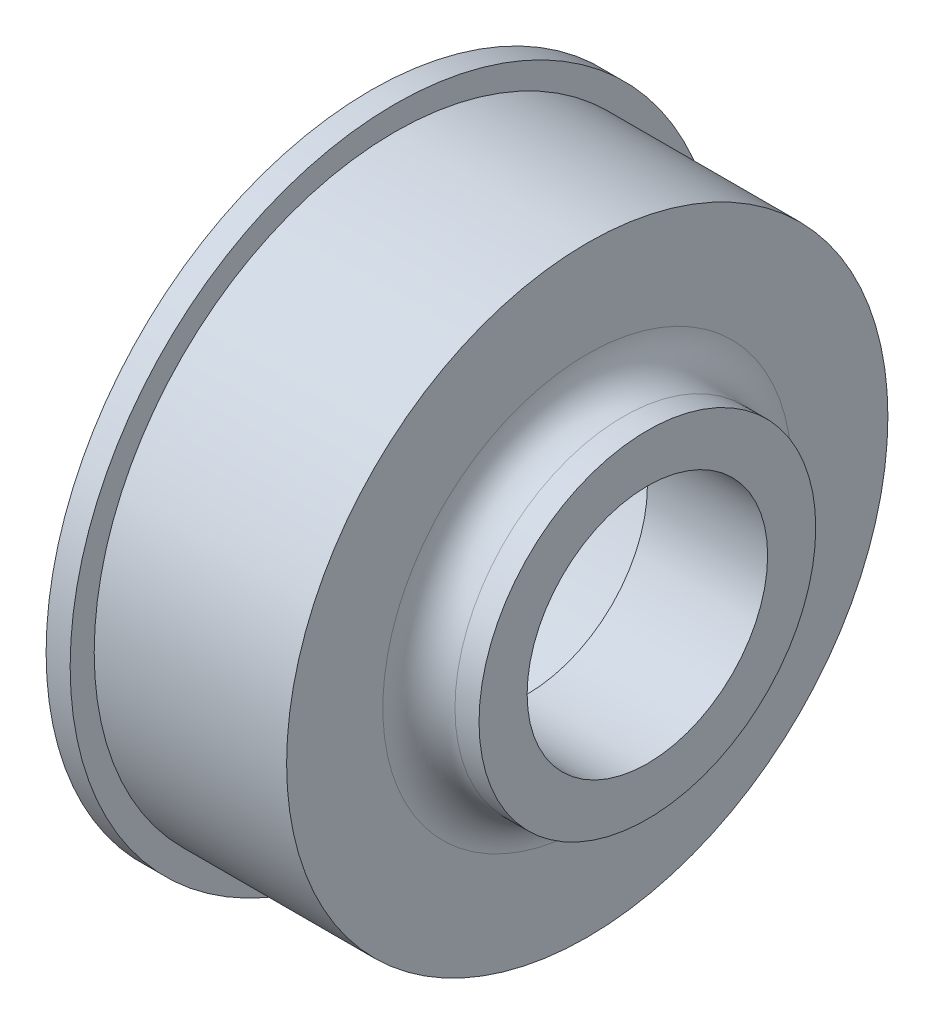
SolidWorks part; units mm, degrees
ref_plane "Front Plane" through (0, 0, 0) normal (0, 0, 1) x (1, 0, 0)
ref_plane "Top Plane" through (0, 0, 0) normal (0, 1, 0) x (1, 0, 0)
ref_plane "Right Plane" through (0, 0, 0) normal (1, 0, 0) x (0, 0, -1)
sketch "Sketch1" plane through (0, 0, 0) normal (0, 0, 1) x (1, 0, 0)
  line L0 (9.2075, 10) -> (9.2075, 14)
  line L1 (9.2075, 0) -> (-11.4201, 0) construction
  line L2 (9.2075, 10) -> (-0.7925, 10)
  line L3 (-0.7925, 10) -> (-0.7925, 20)
  line L4 (-0.7925, 20) -> (-13.7925, 20)
  line L5 (-13.7925, 20) -> (-13.7925, 27)
  line L6 (-13.7925, 27) -> (-11.7925, 27)
  line L7 (-11.7925, 27) -> (-11.7925, 25)
  line L8 (-11.7925, 25) -> (4.2075, 25)
  line L9 (9.2075, 14) -> (7.2075, 14)
  line L10 (4.2075, 17) -> (4.2075, 25)
  arc A0 (7.2075, 14) -> (4.2075, 17) centre (7.2075, 17) cw
  dimension "D11" = 3
  dimension "D1" = 14
  dimension "D2" = 4
  dimension "D3" = 10
  dimension "D4" = 90
  dimension "D5" = 10
  dimension "D6" = 13
  dimension "D7" = 7
  dimension "D8" = 2
  dimension "D9" = 2
  dimension "D10" = 16
revolve "Revolve1" add sketch "Sketch1" angle 360 about L1
